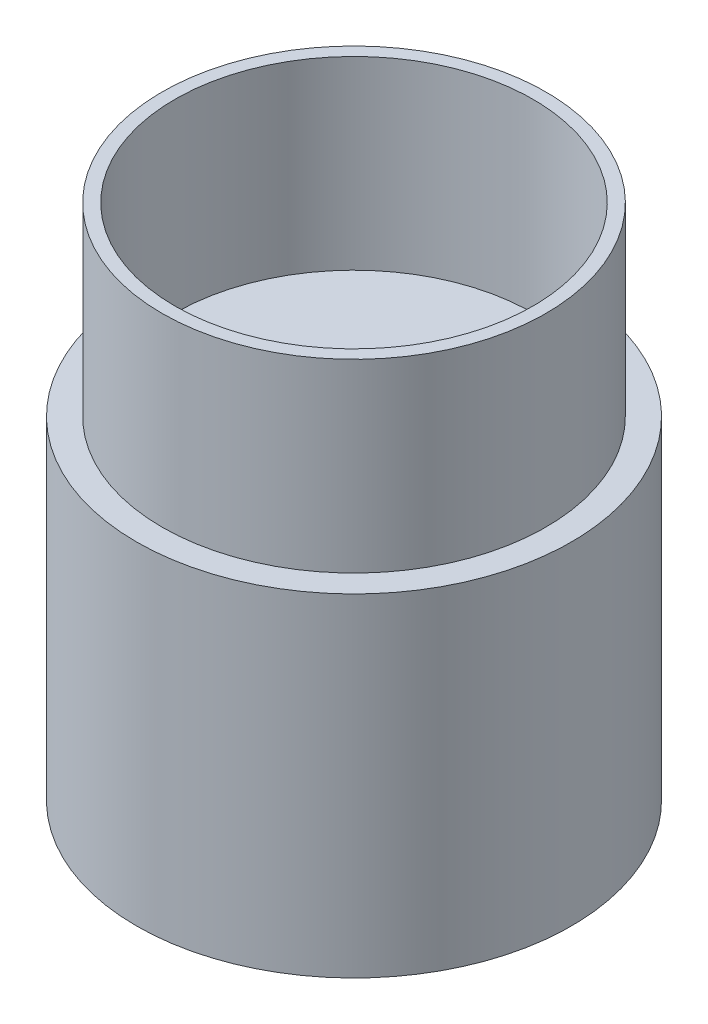
SolidWorks part; units mm, degrees
ref_plane "Front Plane" through (0, 0, 0) normal (0, 0, 1) x (1, 0, 0)
ref_plane "Top Plane" through (0, 0, 0) normal (0, 1, 0) x (1, 0, 0)
ref_plane "Right Plane" through (0, 0, 0) normal (1, 0, 0) x (0, 0, -1)
sketch "Sketch1" plane through (0, 0, 0) normal (0, 1, 0) x (1, 0, 0)
  circle A0 centre (0, 0) radius 85
extrude "Boss-Extrude1" add sketch "Sketch1" along normal blind 130
sketch "Sketch2" plane through (0, 130, 0) normal (0, 1, 0) x (1, 0, 0)
  circle A0 centre (0, 0) radius 26
extrude "Cut-Extrude1" cut sketch "Sketch2" against normal blind 124
sketch "Sketch3" plane through (0, 130, 0) normal (0, 1, 0) x (1, 0, 0)
  circle A0 centre (0, 0) radius 70
  circle A1 centre (0, 0) radius 75
extrude "Boss-Extrude2" add sketch "Sketch3" along normal blind 72.35
